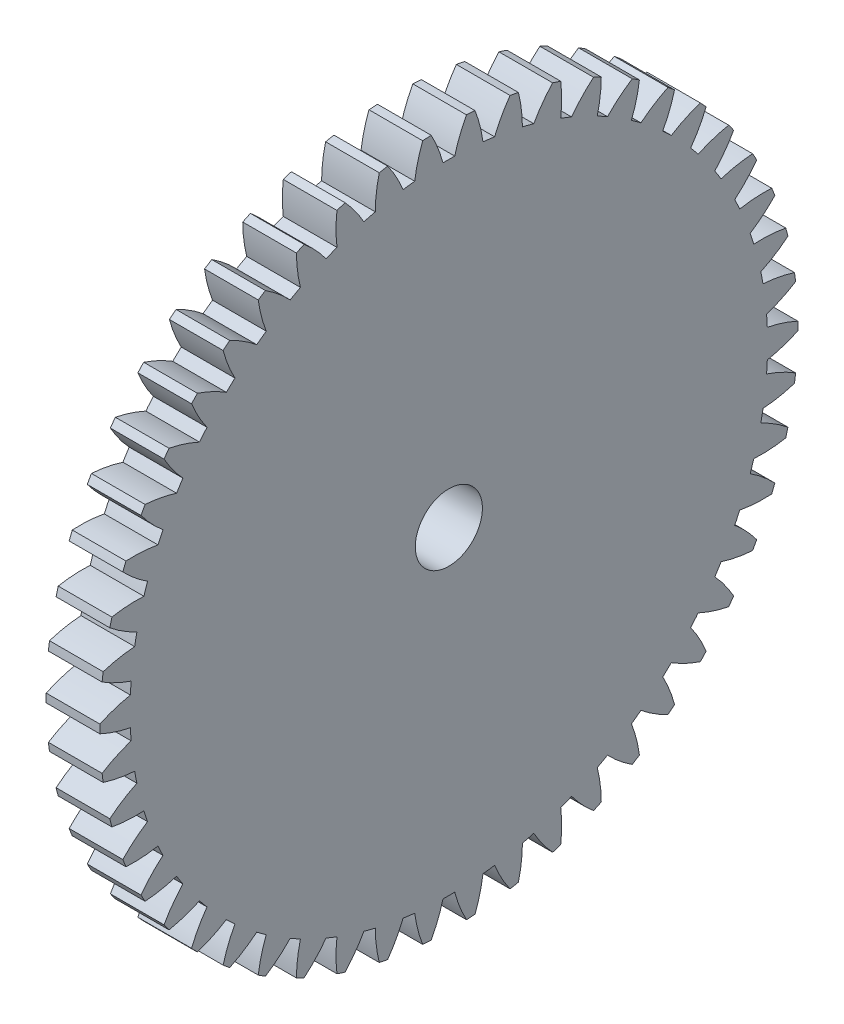
SolidWorks part; units mm, degrees
ref_plane "Plane1" through (0, 0, 0) normal (0, 0, 1) x (1, 0, 0)
ref_plane "Plane2" through (0, 0, 0) normal (0, 1, 0) x (1, 0, 0)
ref_plane "Plane3" through (0, 0, 0) normal (1, 0, 0) x (0, 0, -1)
sketch "HoldingSke" plane through (0, 0, 0) normal (0, 1, 0) x (1, 0, 0)
  line L0 (0, 0) -> (0.6428, -0.766)
  line L1 (-15, 0) -> (100, 0) construction
  line L2 (0, 0) -> (-2.1039, 2.3779)
  line L3 (0, 0) -> (-11.863, 4.5341)
  line L4 (0, 0) -> (5.5511, 6.6156)
  line L5 (0, 0) -> (-46.8476, -17.4728)
  line L6 (0, 0) -> (-3.3159, -2.2372)
  line L7 (-2.1039, 2.3779) -> (8.6586, 51.2059)
  line L8 (-76.2, 54.61) -> (-75.3, 54.61)
  line L9 (-71.009, 38.7566) -> (-53.1078, 45.2721)
  line L10 (-76.2, 71.12) -> (104.1128, 71.12)
  line L11 (0, 0) -> (-4, 0)
  line L12 (-76.2, 101.6) -> (-76.162, 101.6)
  line L13 (24.9733, 27.94) -> (52.9518, 28.4284)
  line L14 (24.9733, 27.94) -> (24.9743, 27.94)
  line L15 (24.9733, 27.94) -> (100.4006, 29.5858)
  line L16 (-63.627, -1) -> (-12.827, -1)
  circle A0 centre (0, 0) radius 2.5
  circle A1 centre (0, 0) radius 23.749
  circle A2 centre (0, 0) radius 37.5
  circle A3 centre (0, 0) radius 2.5
  dimension "MHD" = 47.498
  dimension "Hub_dia" = 75
  dimension "Bore" = 5
  dimension "MBD" = 5
  dimension "Num_teeth" = 50
  dimension "Pitch" = 1
  dimension "Overall_len" = 50
  dimension "Show_teeth" = 50
  dimension "Thickness" = 4
  dimension "OAL" = 50.0001
  dimension "T_dim" = 0.9
  dimension "Ap" = 20
  dimension "H" = 19.05
  dimension "Pitch_radius" = 180.3128
  dimension "Width" = 4
  dimension "Backlash" = 0.038
  dimension "Addendum_fac" = 1
  dimension "Dedendum_fac" = 1.25
  dimension "Clearance_fac" = 0.25
  dimension "Dedendum_add" = 0.001
  dimension "Module" = 1
sketch "BasProSke" plane through (0, 0, 0) normal (0, 1, 0) x (1, 0, 0)
  line L0 (-10, 0) -> (60, 0) construction
  line L1 (0, 0) -> (0, 26)
  line L2 (0, 0) -> (4, 0)
  line L3 (4, 0) -> (4, 26)
  line L4 (4, 26) -> (0, 26)
  dimension "Thickness" = 4
  dimension "Diameter" = 52
revolve "Base-Revolve" add sketch "BasProSke" angle 360 about L0
sketch "TooCutSke" plane through (0, 0, 0) normal (1, 0, 0) x (0, 0, -1)
  line L1 (0, 0) -> (0, 107) construction
  line L2 (0, 0) -> (-0.8518, 24.9855) construction
  line L3 (0, 0) -> (-3.1382, 49.8807) construction
  line L4 (-0.8518, 24.9855) -> (-1.5691, 24.9404) construction
  arc A0 (0.4377, 23.745) -> (-0.4377, 23.745) centre (0, 0) ccw
  arc A1 (1.3294, 25.9914) -> (-1.3294, 25.9914) centre (0, 0) ccw
  circle A2 centre (0, 0) radius 25 construction
  circle A3 centre (0, 0) radius 23.4923 construction
  arc A4 (-0.4377, 23.745) -> (-1.3294, 25.9914) centre (-10.1099, 21.2056) ccw
  arc A5 (1.3294, 25.9914) -> (0.4377, 23.745) centre (10.1099, 21.2056) ccw
  dimension "Root_dia" = 47.498
  dimension "Overcut_dia" = 52.0508
  dimension "Pitch_dia" = 50
  dimension "Base_dia" = 46.9846
  dimension "Flank_rad" = 10
  dimension "Half_ang" = 3.6
  dimension "Half_CT" = 0.7188
extrude "ToothCut" cut sketch "TooCutSke" along normal through all
fillet "Breaks" [suppressed] radius 0.02
fillet "RootFillets" [suppressed] radius 0.251
pattern_circular "TeethCuts" count 50 every 7.2 about axis through (-10, 0, 0) along (1, 0, 0) of "ToothCut", "RootFillets", "Breaks"
sketch "HubNeaOneSke" plane through (0, 0, 0) normal (-1, 0, 0) x (0, 0, 1)
  circle A0 centre (0, 0) radius 23.749
  dimension "Diameter" = 47.498
extrude "HubNearOne" [suppressed] add sketch "HubNeaOneSke" along normal blind 46.0001
sketch "HubNeaBotSke" plane through (0, 0, 0) normal (-1, 0, 0) x (0, 0, 1)
  circle A0 centre (0, 0) radius 23.749
  dimension "Diameter" = 47.498
extrude "HubNearBoth" [suppressed] add sketch "HubNeaBotSke" along normal blind 23
ref_plane "FarPln" through (4, 0, 0) normal (1, 0, 0) x (0, 0, -1)
sketch "HubFarSke" plane through (4, 0, 0) normal (1, 0, 0) x (0, 0, -1)
  circle A0 centre (0, 0) radius 23.749
  dimension "Diameter" = 47.498
extrude "HubFar" [suppressed] add sketch "HubFarSke" along normal blind 23
sketch "BorSke" plane through (0, 0, 0) normal (1, 0, 0) x (0, 0, -1)
  circle A0 centre (0, 0) radius 2.5
  dimension "Diameter" = 5
extrude "Bore" cut sketch "BorSke" along normal mid plane 100.0001
sketch "KeySke" plane through (0, 0, 0) normal (1, 0, 0) x (0, 0, -1)
  line L0 (-1, 0) -> (-1, 3.4)
  line L1 (-1, 3.4) -> (1, 3.4)
  line L2 (1, 3.4) -> (1, 0)
  line L3 (0, 0) -> (0, 34) construction
  line L4 (-1, 0) -> (1, 0)
  dimension "Offset" = 3.4
  dimension "Width" = 2
extrude "Keyway" [suppressed] cut sketch "KeySke" along normal mid plane 100.0001
pattern_circular "Keyway2" [suppressed] count 2 every 90 about axis through (-10, 0, 0) along (1, 0, 0)
equation "' \"Module@HoldingSke\" = 6.35"
equation "' \"Num_teeth@HoldingSke\" = 12"
equation "' \"Ap@HoldingSke\" =  20"
equation "' \"Ap@HoldingSke\" = 20"
equation "' \"Width@HoldingSke\" = 0.5 * 25.4"
equation "' \"Hub_dia@HoldingSke\"= 1 * 25.4"
equation "' \"Hub_dia@HoldingSke\" = 1 * 25.4"
equation "' \"Overall_len@HoldingSke\" = 1.0 * 25.4"
equation "' \"Bore@HoldingSke\" = 0.75 * 25.4"
equation "' \"T_dim@HoldingSke\" = 0.1 * 25.4"
equation "' \"Width@KeySke\" = 0.25 * 25.4"
equation "' \"Show_teeth@HoldingSke\" = 13"
equation "' \"Backlash@HoldingSke\" = 0.009 * 25.4"
equation "' \"Addendum_fac@HoldingSke\" = 1.0"
equation "' \"Dedendum_fac@HoldingSke\" = 1.25"
equation "' \"Dedendum_add@HoldingSke\" = 0.00005 * 25.4"
equation "' \"Clearance_fac@HoldingSke\" = 0.25"
equation "\"Pitch@HoldingSke\" = 1 / \"Module@HoldingSke\""
equation "\"Overcut_dia@TooCutSke\" = (\"Num_teeth@HoldingSke\" + 2 * \"Addendum_fac@HoldingSke\") / \"Pitch@HoldingSke\" + 0.002 * 25.4"
equation "\"Pitch_dia@TooCutSke\" = \"Num_teeth@HoldingSke\" / \"Pitch@HoldingSke\""
equation "\"Base_dia@TooCutSke\" = \"Num_teeth@HoldingSke\" / \"Pitch@HoldingSke\" * cos((\"Ap@HoldingSke\"  * 3.14159265 / 180))"
equation "\"Root_dia@TooCutSke\" = (\"Num_teeth@HoldingSke\" + 2) / \"Pitch@HoldingSke\" - 2 * (\"Addendum_fac@HoldingSke\" + \"Dedendum_fac@HoldingSke\") / \"Pitch@HoldingSke\" - \"Dedendum_add@HoldingSke\" * 2"
equation "\"Half_ang@TooCutSke\" = 180 / \"Num_teeth@HoldingSke\""
equation "\"Half_CT@TooCutSke\" = \"Num_teeth@HoldingSke\" / \"Pitch@HoldingSke\" * sin((3.14159265 / 2 / \"Num_teeth@HoldingSke\")) / 2 - 7 * \"Backlash@HoldingSke\" / 4"
equation "\"Flank_rad@TooCutSke\" = \"Num_teeth@HoldingSke\" / \"Pitch@HoldingSke\" / 5"
equation "\"Radius@RootFillets\" = \"Clearance_fac@HoldingSke\" / \"Pitch@HoldingSke\" + \"Dedendum_add@HoldingSke\""
equation "\"Break_rad@Breaks\" = 0.02 / \"Pitch@HoldingSke\""
equation "\"Thickness@HoldingSke\" = \"Width@HoldingSke\""
equation "\"OAL@HoldingSke\" = \"Thickness@HoldingSke\""
equation "\"MHD@HoldingSke\" = (\"Num_teeth@HoldingSke\" + 2) / \"Pitch@HoldingSke\" - 2 * (\"Addendum_fac@HoldingSke\" + \"Dedendum_fac@HoldingSke\")  / \"Pitch@HoldingSke\" - \"Dedendum_add@HoldingSke\" * 2"
equation "\"MBD@HoldingSke\" = (\"Num_teeth@HoldingSke\" + 2) / \"Pitch@HoldingSke\" - 2 * (\"Addendum_fac@HoldingSke\" + \"Dedendum_fac@HoldingSke\")  / \"Pitch@HoldingSke\" - \"Dedendum_add@HoldingSke\" * 2 - 0.002 * 25.4"
equation "\"MHD@HoldingSke\" = ((sgn( \"MHD@HoldingSke\" - \"Hub_dia@HoldingSke\" )-1)*( \"MHD@HoldingSke\" - \"Hub_dia@HoldingSke\" ))/-2+ \"Hub_dia@HoldingSke\""
equation "\"MBD@HoldingSke\" = ((sgn( \"MBD@HoldingSke\" - \"Bore@HoldingSke\" )-1)*( \"MBD@HoldingSke\" - \"Bore@HoldingSke\" ))/-2+ \"Bore@HoldingSke\""
equation "\"OAL@HoldingSke\" = ((sgn( \"OAL@HoldingSke\" - \"Overall_len@HoldingSke\" )+1)*( \"OAL@HoldingSke\" - \"Overall_len@HoldingSke\" ))/2 + \"Overall_len@HoldingSke\" + 0.000002 * 25.4"
equation "\"Num_teeth@TeethCuts\" = int( \"Show_teeth@HoldingSke\" ) + 1"
equation "\"Num_teeth@TeethCuts\" = ((sgn( \"Num_teeth@TeethCuts\" - \"Num_teeth@HoldingSke\" )-1)*( \"Num_teeth@TeethCuts\" - \"Num_teeth@HoldingSke\" ))/-2+ \"Num_teeth@HoldingSke\""
equation "\"Num_teeth@TeethCuts\" = ((sgn( \"Num_teeth@TeethCuts\" - 2.0)+1)*( \"Num_teeth@TeethCuts\" - 2.0))/2 +2.0"
equation "\"Angle@TeethCuts\" = 360.0 / \"Num_teeth@HoldingSke\""
equation "\"Diameter@BasProSke\" = (\"Num_teeth@HoldingSke\" + 2 * \"Addendum_fac@HoldingSke\") / \"Pitch@HoldingSke\""
equation "\"Thickness@BasProSke\"  = \"Thickness@HoldingSke\""
equation "' \"Fillet_rad@BasProSke\" =  \"Thickness@HoldingSke\" * 0.05"
equation "' \"Fillet_rad@BasProSke\" = \"Thickness@HoldingSke\" * 0.05"
equation "\"MHD@HoldingSke\" = ((sgn( \"MHD@HoldingSke\" - \"Root_dia@TooCutSke\" )-1)*( \"MHD@HoldingSke\" - \"Root_dia@TooCutSke\" ))/-2+ \"Root_dia@TooCutSke\""
equation "\"Diameter@HubNeaOneSke\" = \"MHD@HoldingSke\""
equation "\"Length@HubNearOne\" = \"OAL@HoldingSke\" - \"Thickness@BasProSke\""
equation "\"Diameter@HubNeaBotSke\" = \"MHD@HoldingSke\""
equation "\"Length@HubNearBoth\" = ( \"OAL@HoldingSke\" - \"Thickness@BasProSke\" ) / 2.0"
equation "\"Thickness@FarPln\" = \"Thickness@BasProSke\""
equation "\"Diameter@HubFarSke\" = \"MHD@HoldingSke\""
equation "\"Length@HubFar\" = ( \"OAL@HoldingSke\" - \"Thickness@BasProSke\" ) / 2.0"
equation "\"Diameter@BorSke\" = \"MBD@HoldingSke\""
equation "\"D1@Bore\" = \"OAL@HoldingSke\" * 2.0"
equation "\"D1@Keyway\" = \"OAL@HoldingSke\" * 2.0"
equation "\"Offset@KeySke\" = \"T_dim@HoldingSke\" + \"MBD@HoldingSke\" / 2.0"
